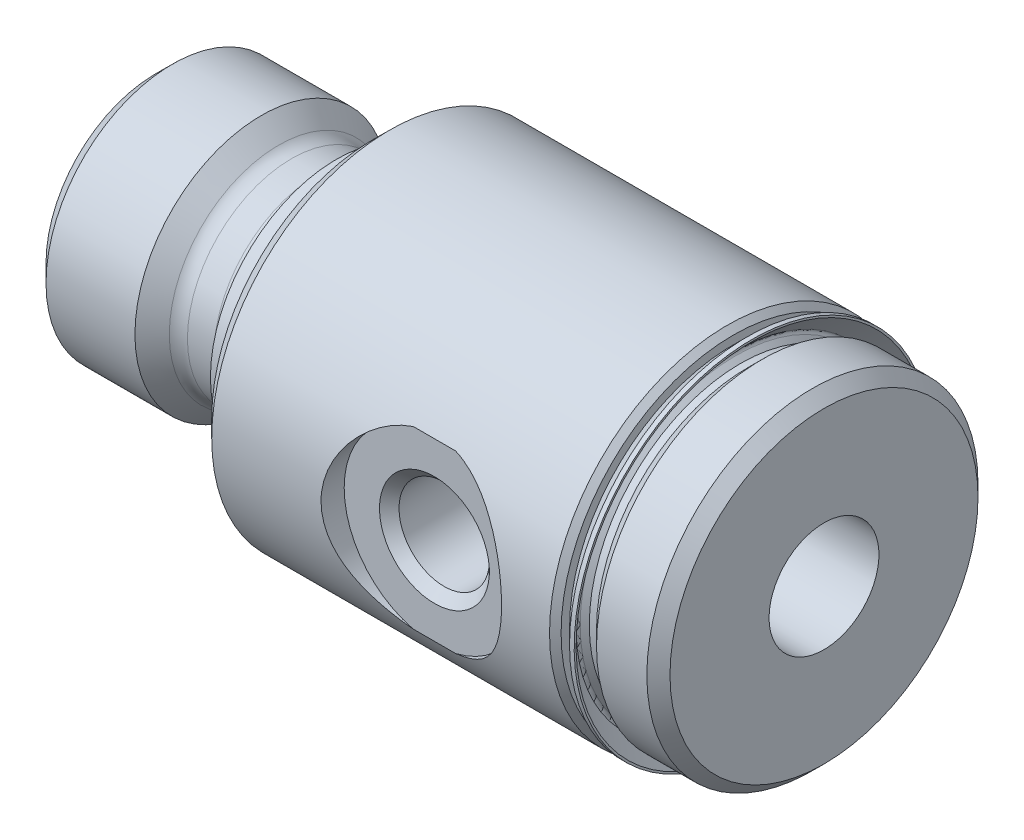
SolidWorks part; units mm, degrees
ref_plane "Front Plane" through (0, 0, 0) normal (0, 0, 1) x (1, 0, 0)
ref_plane "Top Plane" through (0, 0, 0) normal (0, 1, 0) x (1, 0, 0)
ref_plane "Right Plane" through (0, 0, 0) normal (1, 0, 0) x (0, 0, -1)
ref_plane "Plane1" through (0, 0, 0) normal (0, 0, 1) x (1, 0, 0)
sketch "Sketch1" plane through (0, 0, 0) normal (0, 0, 1) x (1, 0, 0)
  line L0 (0, 0) -> (0, 4.8006)
  line L1 (0, 4.8006) -> (0.7556, 5.5563)
  line L2 (0.7556, 5.5563) -> (4.6603, 5.5563)
  line L3 (4.6603, 5.5563) -> (5.4181, 4.8042)
  line L4 (5.9817, 4.572) -> (7.1501, 4.572)
  line L5 (7.9502, 5.3721) -> (7.9502, 5.5309)
  line L6 (7.9502, 5.5309) -> (9.525, 5.5309)
  line L7 (9.525, 5.5309) -> (9.525, 0)
  line L8 (9.525, 0) -> (0, 0)
  line L9 (9.525, 0) -> (0, 0) construction
  arc A0 (5.4181, 4.8042) -> (5.9817, 4.572) centre (5.9817, 5.3721) ccw
  arc A1 (7.1501, 4.572) -> (7.9502, 5.3721) centre (7.1501, 5.3721) ccw
revolve "Revolve1" add sketch "Sketch1" angle 360 about L9
cosmetic thread "Cosmetic Thread1" parameters "D1"=5.4159, "D2"=9.6012
ref_plane "Plane2" through (0, 0, 0) normal (0, 0, 1) x (1, 0, 0)
sketch "Sketch2" plane through (0, 0, 0) normal (0, 0, 1) x (1, 0, 0)
  line L0 (9.525, 0) -> (9.525, 7.0485)
  line L1 (9.525, 7.0485) -> (10.287, 7.8105)
  line L2 (10.287, 7.8105) -> (25.1206, 7.8105)
  line L3 (25.1206, 7.8105) -> (25.3746, 7.5565)
  line L4 (25.3746, 7.5565) -> (25.3746, 6.6357)
  line L5 (25.3746, 6.6357) -> (26.0096, 6.6357)
  line L6 (26.0096, 6.6357) -> (26.6446, 7.2708)
  line L7 (26.6446, 7.2708) -> (28.8544, 7.2708)
  line L8 (28.8544, 7.2708) -> (29.3624, 6.7627)
  line L9 (29.3624, 6.7627) -> (29.3624, 0)
  line L10 (29.3624, 0) -> (9.525, 0)
  line L11 (29.3624, 0) -> (9.525, 0) construction
revolve "Revolve2" add sketch "Sketch2" angle 360 about L11
ref_plane "Plane3" through (0, 0, 0) normal (0, 0, 1) x (1, 0, 0)
sketch "Sketch3" plane through (0, 0, 0) normal (0, 0, 1) x (1, 0, 0)
  line L0 (0, 0) -> (0, 2.921)
  line L1 (0, 2.921) -> (0.508, 2.413)
  line L2 (0.508, 2.413) -> (29.3624, 2.413)
  line L3 (29.3624, 2.413) -> (29.3624, 0)
  line L4 (29.3624, 0) -> (0, 0)
  line L5 (29.3624, 0) -> (0, 0) construction
revolve "Cut-Revolve1" cut sketch "Sketch3" angle 360 about L5
ref_plane "Plane4" through (0, 0, 0) normal (0, 1, 0) x (1, 0, 0)
sketch "Sketch4" plane through (0, 0, 0) normal (0, 1, 0) x (1, 0, 0)
  line L0 (19.05, 1.016) -> (21.0337, 1.016)
  line L1 (21.0337, 1.016) -> (21.0337, -6.3652)
  line L2 (21.0337, -6.3652) -> (21.463, -6.7945)
  line L3 (21.463, -6.7945) -> (23.0124, -6.7945)
  line L4 (23.0124, -6.7945) -> (23.0124, -7.8105)
  line L5 (23.0124, -7.8105) -> (19.05, -7.8105)
  line L6 (19.05, -7.8105) -> (19.05, 1.016)
  line L7 (19.05, -7.8105) -> (19.05, 1.016) construction
revolve "Cut-Revolve2" cut sketch "Sketch4" angle 360 about L7
ref_plane "Plane5" through (0, 0, 0) normal (0, 0, 1) x (1, 0, 0)
sketch "Sketch5" plane through (0, 0, 0) normal (0, 0, 1) x (1, 0, 0)
  line L0 (25.3746, 7.1861) -> (25.3746, 6.3818)
  line L1 (25.3746, 6.3818) -> (26.0096, 6.3818)
  line L2 (26.0096, 6.3818) -> (26.0096, 6.6357)
  line L3 (26.0096, 6.6357) -> (25.6921, 6.6357)
  line L4 (25.6921, 6.6357) -> (25.4916, 6.8362)
  line L5 (25.4916, 7.0158) -> (26.2022, 7.7263)
  line L6 (26.2022, 7.7263) -> (26.2022, 7.8105)
  line L7 (26.2022, 7.8105) -> (25.999, 7.8105)
  line L8 (25.999, 7.8105) -> (25.3746, 7.1861)
  line L9 (26.0096, 0) -> (25.3746, 0) construction
  arc A0 (25.4916, 6.8362) -> (25.4916, 7.0158) centre (25.5814, 6.926) cw
revolve "Revolve3" add sketch "Sketch5" angle 360 about L9
